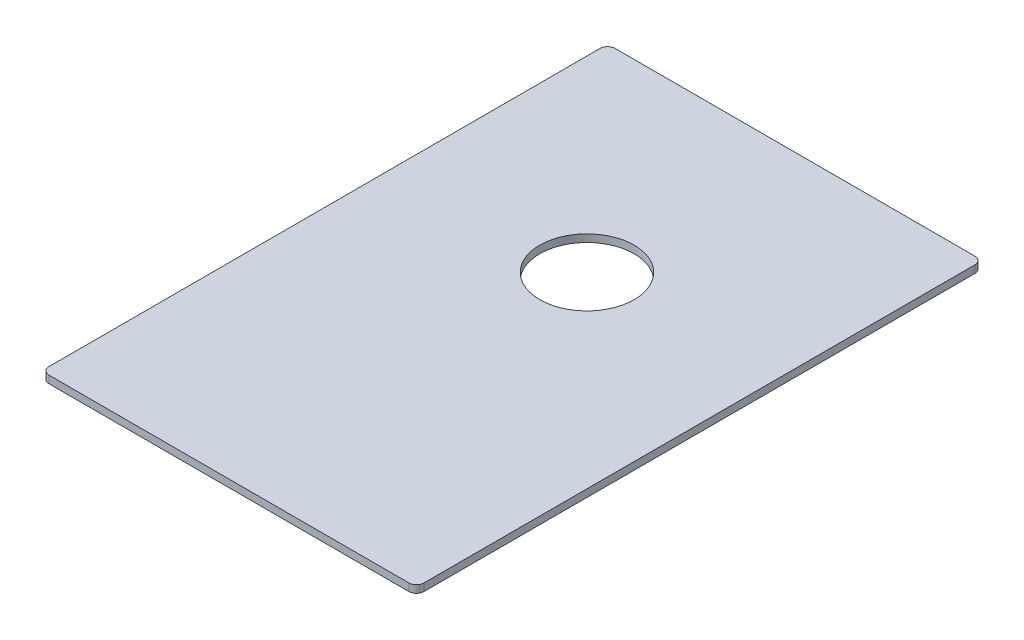
SolidWorks part; units mm, degrees
ref_plane "Ön Düzlem" through (0, 0, 0) normal (0, 0, 1) x (1, 0, 0)
ref_plane "Üst Düzlem" through (0, 0, 0) normal (0, 1, 0) x (1, 0, 0)
ref_plane "Sağ Düzlem" through (0, 0, 0) normal (1, 0, 0) x (0, 0, -1)
sketch "Sketch1" plane through (0, 0, 0) normal (0, 1, 0) x (1, 0, 0)
  line L1 (-250, -377.5) -> (250, -377.5)
  line L2 (-250, -377.5) -> (-250, 377.5)
  line L3 (-250, 377.5) -> (250, 377.5)
  line L4 (250, -377.5) -> (250, 377.5)
  line L5 (-250, -377.5) -> (250, 377.5) construction
  line L6 (-250, 377.5) -> (250, -377.5) construction
  point P0 (0, 0)
  dimension "D1" = 500
  dimension "D2" = 755
extrude "Boss-Extrude1" add sketch "Sketch1" along normal blind 10 contours L2 L3 L4 L1
sketch "Sketch3" plane through (0, 0, 0) normal (0, 1, 0) x (1, 0, 0)
  circle A0 centre (0, 100) radius 63
  dimension "D1" = 100
extrude "Cut-Extrude10" cut sketch "Sketch3" along normal through all
fillet "Fillet1" radius 10 4 edges at (-250, 5, -377.5) (-250, 5, 377.5) (250, 5, 377.5) (250, 5, -377.5)
